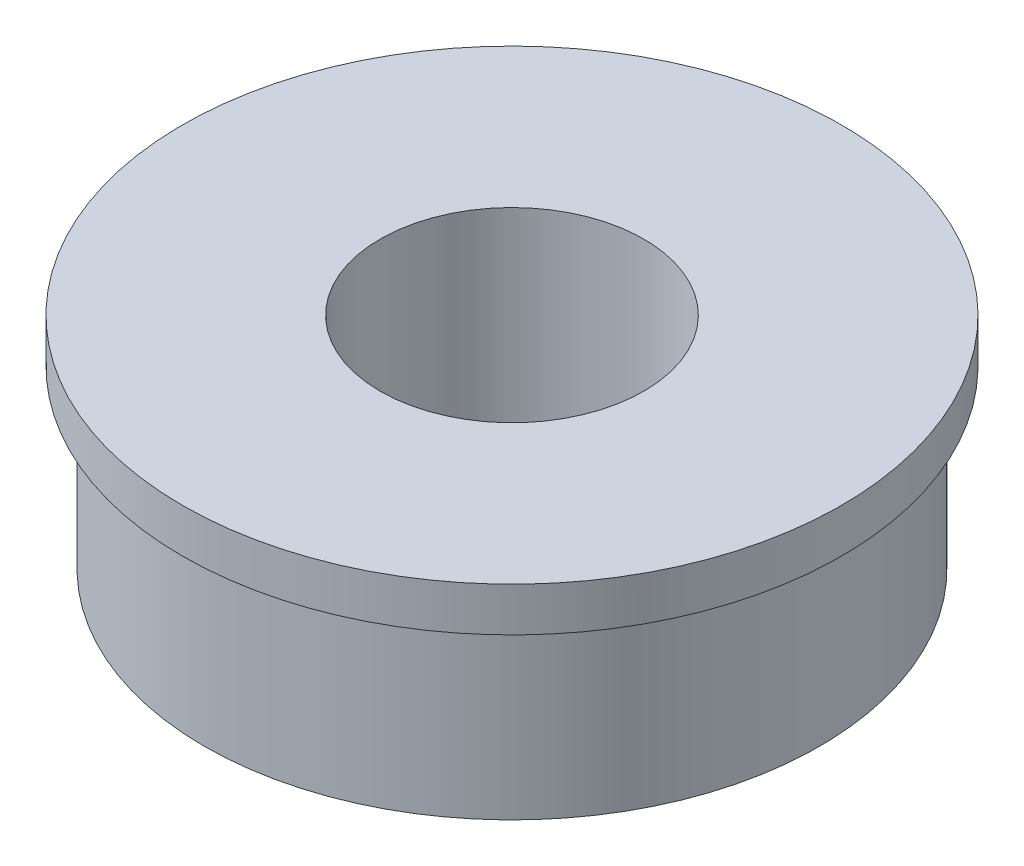
SolidWorks part; units mm, degrees
ref_plane "Front Plane" through (0, 0, 0) normal (0, 0, 1) x (1, 0, 0)
ref_plane "Top Plane" through (0, 0, 0) normal (0, 1, 0) x (1, 0, 0)
ref_plane "Right Plane" through (0, 0, 0) normal (1, 0, 0) x (0, 0, -1)
sketch "Sketch1" plane through (0, 0, 0) normal (0, 1, 0) x (1, 0, 0)
  circle A0 centre (0, 0) radius 7.5
  circle A1 centre (0, 0) radius 3
extrude "Boss-Extrude1" add sketch "Sketch1" against normal blind 5
sketch "Sketch2" plane through (0, -5, 0) normal (0, -1, 0) x (1, 0, 0)
  circle A0 centre (0, 0) radius 7
  circle A1 centre (0, 0) radius 7.5
extrude "Cut-Extrude2" cut sketch "Sketch2" against normal blind 4
